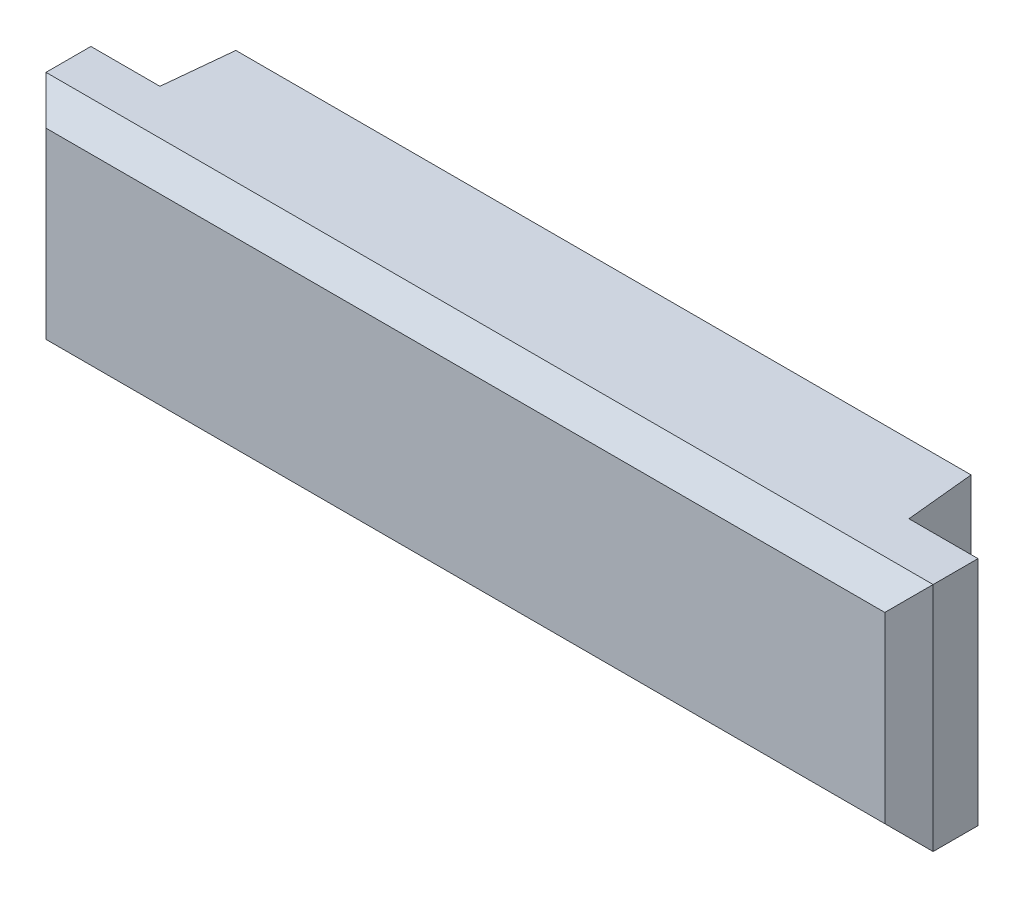
SolidWorks part; units mm, degrees
ref_plane "Front Plane" through (0, 0, 0) normal (0, 0, 1) x (1, 0, 0)
ref_plane "Top Plane" through (0, 0, 0) normal (0, 1, 0) x (1, 0, 0)
ref_plane "Right Plane" through (0, 0, 0) normal (1, 0, 0) x (0, 0, -1)
sketch "Sketch1" plane through (0, 0, 0) normal (0, 0, 1) x (1, 0, 0)
  line L1 (10.65, -2.35) -> (-10.65, -2.35)
  line L2 (10.65, -2.35) -> (10.65, 2.35)
  line L3 (10.65, 2.35) -> (-10.65, 2.35)
  line L4 (-10.65, -2.35) -> (-10.65, 2.35)
  line L5 (10.65, -2.35) -> (-10.65, 2.35) construction
  line L6 (10.65, 2.35) -> (-10.65, -2.35) construction
  point P0 (0, 0)
  point P6 (0, 0)
  dimension "D1" = 21.3
  dimension "D2" = 4.7
ref_plane "Plane1" through (0, 0, 2) normal (0, 0, 1) x (1, 0, 0)
sketch "Sketch2" plane through (0, 0, 2) normal (0, 0, 1) x (1, 0, 0)
  line L1 (-10.85, -2.35) -> (10.85, -2.35)
  line L2 (-10.85, -2.35) -> (-10.85, 2.35)
  line L3 (-10.85, 2.35) -> (10.85, 2.35)
  line L4 (10.85, -2.35) -> (10.85, 2.35)
  line L5 (-10.85, -2.35) -> (10.85, 2.35) construction
  line L6 (-10.85, 2.35) -> (10.85, -2.35) construction
  point P0 (0, 0)
  point P5 (10.6, 0.3197)
  dimension "D1" = 21.7
loft "Loft1" add profiles "Sketch2", "Sketch1"
sketch "Sketch3" plane through (0, 0, 2) normal (0, 0, 1) x (1, 0, 0)
  line L0 (10.85, -2.35) -> (10.85, 2.35) construction
  line L1 (-12.85, 2.35) -> (12.85, 2.35)
  line L2 (-12.85, 2.35) -> (-12.85, -4.35)
  line L3 (-12.85, -4.35) -> (12.85, -4.35)
  line L4 (12.85, 2.35) -> (12.85, -4.35)
  point P4 (0, -4.35)
  point P6 (0, 0)
  dimension "D1" = 2
  dimension "D2" = 2
extrude "Boss-Extrude1" add sketch "Sketch3" along normal blind 2
chamfer "Chamfer1" distance 0.7 angle 45 4 edges at (0, 2.35, 4) (12.85, -1, 4) (0, -4.35, 4) (-12.85, -1, 4)
equation "\"D2@Sketch3\"=\"D1@Sketch3\""
